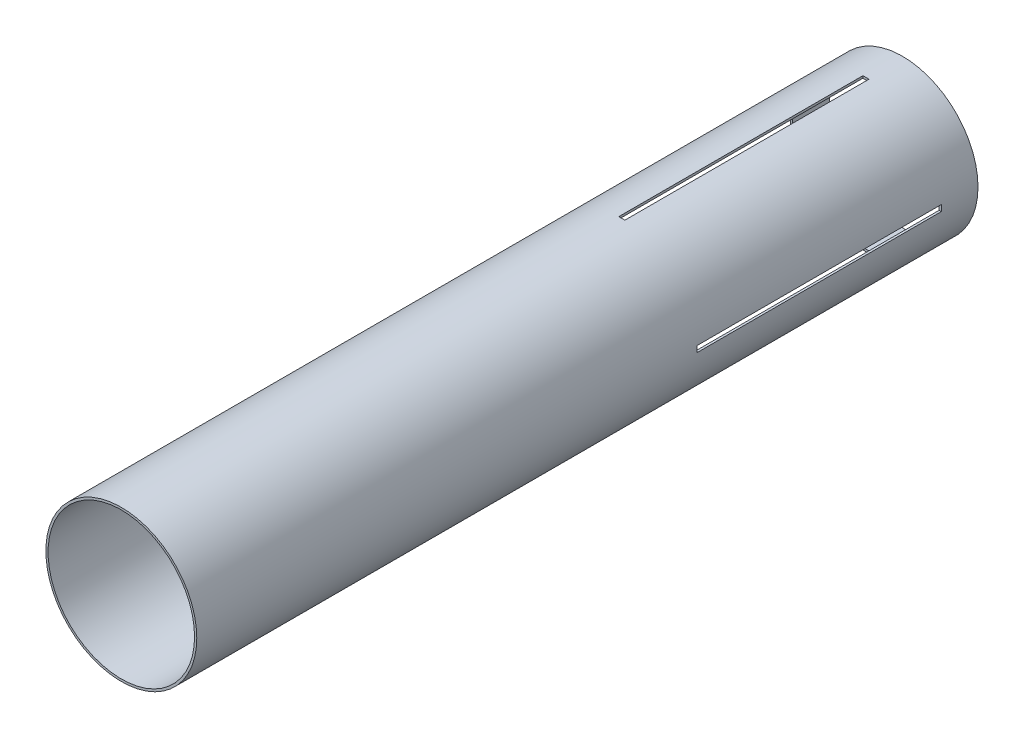
SolidWorks part; units mm, degrees
ref_plane "Front Plane" through (0, 0, 0) normal (0, 0, 1) x (1, 0, 0)
ref_plane "Top Plane" through (0, 0, 0) normal (0, 1, 0) x (1, 0, 0)
ref_plane "Right Plane" through (0, 0, 0) normal (1, 0, 0) x (0, 0, -1)
sketch "Sketch1" plane through (0, 0, 0) normal (0, 0, 1) x (1, 0, 0)
  circle A0 centre (0, 0) radius 39.2557
  circle A1 centre (0, 0) radius 38.1
  dimension "D1" = 76.2
  dimension "D2" = 78.5114
extrude "Boss-Extrude1" add sketch "Sketch1" along normal mid plane 406.4
sketch "Sketch3" plane through (0, 0, 0) normal (0, 1, 0) x (1, 0, 0)
  line L0 (39.2557, 203.2) -> (-39.2557, 203.2) construction
  line L1 (1.5875, 57.15) -> (-1.5875, 57.15)
  line L2 (1.5875, 57.15) -> (1.5875, 184.15)
  line L3 (1.5875, 184.15) -> (-1.5875, 184.15)
  line L4 (-1.5875, 57.15) -> (-1.5875, 184.15)
  line L5 (1.5875, 57.15) -> (-1.5875, 184.15) construction
  line L6 (1.5875, 184.15) -> (-1.5875, 57.15) construction
  line L7 (39.2557, 203.2) -> (-39.2557, 203.2) construction
  point P0 (0, 120.65)
  dimension "D1" = 3.175
  dimension "D2" = 127
  dimension "D3" = 19.05
extrude "Cut-Extrude1" cut sketch "Sketch3" along normal through all
pattern_circular "CirPattern1" count 4 over 360 about axis through (0, 0, 0) along (0, 0, 1) of "Cut-Extrude1"
equation "\"AIRFRAME_OD\"= 3.091in"
equation "\"AIRFRAME_ID\"= 3.00in"
equation "\"FLAT_T\"= 0.125in"
equation "\"NOSE_EXP_L\"= 3.5in"
equation "\"NOSE_SHOULDER_L\"= 5in"
equation "\"MAIN_L\"= 30in"
equation "\"RECO_COUP_L\"= 6in"
equation "\"RECO_SWITCH_L\"= 1.5in"
equation "\"DROGUE_L\"= 14in"
equation "\"ATS_FORE_COUP_L\"= 4in"
equation "\"ATS_AFT_COUP_L\"= 2.5in"
equation "\"LOWER_L\"= 16in"
equation "\"FIN_N\"= 4"
equation "\"CR_AFT_X\"= 0.5in"
equation "\"CR_FORE_X\"= 6in"
equation "\"D1@Sketch1\"=\"AIRFRAME_ID\""
equation "\"D2@Sketch1\"=\"AIRFRAME_OD\""
equation "\"D1@Boss-Extrude1\"=\"LOWER_L\""
equation "\"FIN_ROOT\"= 5in"
equation "\"FIN_X\"= 0.75in"
equation "\"MOTOR_OD\"= 2.25in"
equation "\"MOTOR_ID\"= 2.126in"
equation "\"D1@Sketch3\"=\"FLAT_T\""
equation "\"D2@Sketch3\"=\"FIN_ROOT\""
equation "\"D3@Sketch3\"=\"FIN_X\""
equation "\"D1@CirPattern1\"=\"FIN_N\""
